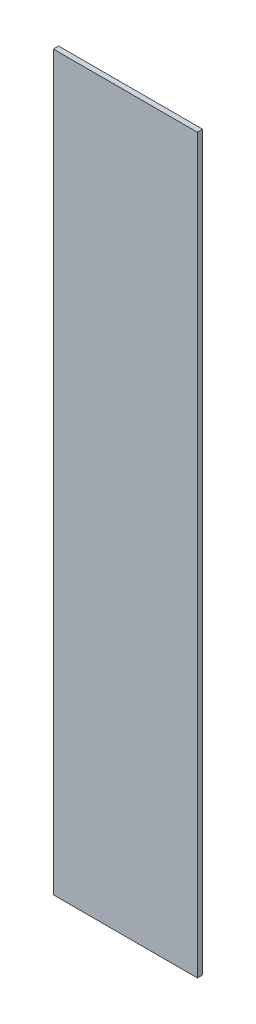
SolidWorks part; units mm, degrees
material "OSB_Plywood"
ref_plane "Front Plane" through (0, 0, 0) normal (0, 0, 1) x (1, 0, 0)
ref_plane "Top Plane" through (0, 0, 0) normal (0, 1, 0) x (1, 0, 0)
ref_plane "Right Plane" through (0, 0, 0) normal (1, 0, 0) x (0, 0, -1)
sketch "Sketch1" plane through (0, 0, 0) normal (0, 0, 1) x (1, 0, 0)
  line L1 (0, 0) -> (304.8, 0)
  line L2 (0, 0) -> (0, 1549.4)
  line L3 (0, 1549.4) -> (304.8, 1549.4)
  line L4 (304.8, 0) -> (304.8, 1549.4)
  dimension "D1" = 304.8
  dimension "D2" = 1549.4
extrude "Boss-Extrude1" add sketch "Sketch1" along normal blind 11.1125
